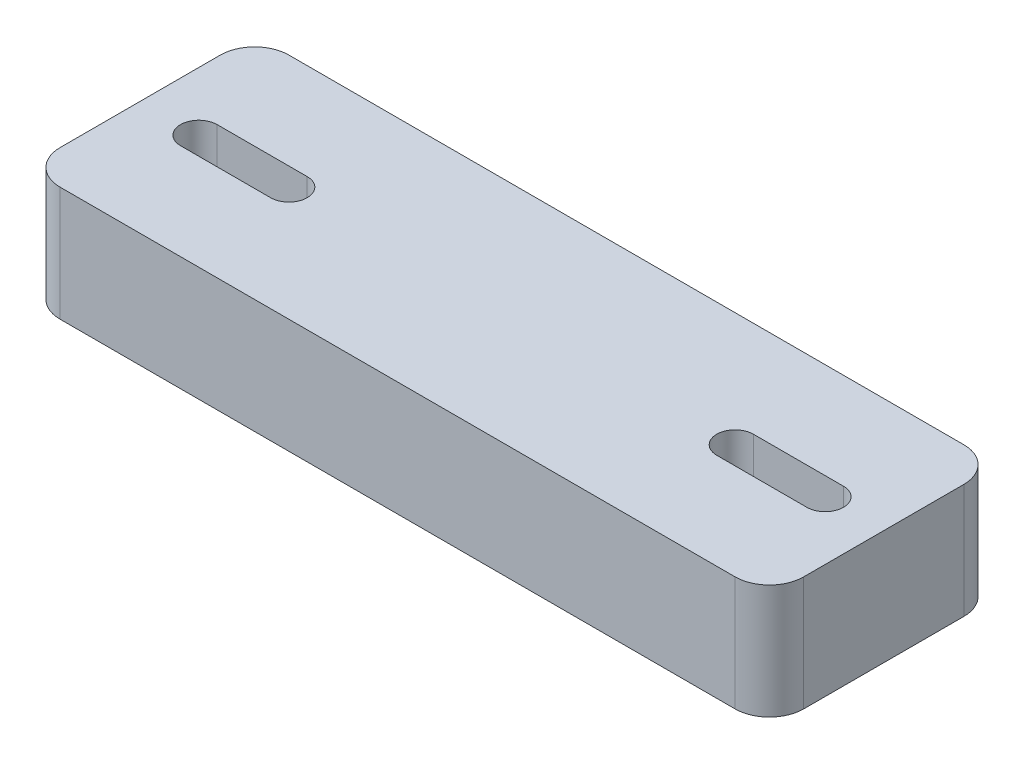
SolidWorks part; units mm, degrees
ref_plane "前视基准面" through (0, 0, 0) normal (0, 0, 1) x (1, 0, 0)
ref_plane "上视基准面" through (0, 0, 0) normal (0, 1, 0) x (1, 0, 0)
ref_plane "右视基准面" through (0, 0, 0) normal (1, 0, 0) x (0, 0, -1)
sketch "草图1" plane through (0, 0, 0) normal (0, 1, 0) x (1, 0, 0)
  line L1 (-32.5, 10) -> (32.5, 10)
  line L2 (-32.5, 10) -> (-32.5, -10)
  line L3 (-32.5, -10) -> (32.5, -10)
  line L4 (32.5, 10) -> (32.5, -10)
  line L5 (-32.5, 10) -> (32.5, -10) construction
  line L6 (-32.5, -10) -> (32.5, 10) construction
  point P0 (0, 0)
  dimension "D1" = 65
  dimension "D2" = 20
extrude "凸台-拉伸1" add sketch "草图1" along normal blind 10
sketch "草图2" plane through (0, 10, 0) normal (0, 1, 0) x (1, 0, 0)
  line L0 (0, 0) -> (0, -10) construction
  line L1 (-32.5, -10) -> (32.5, -10) construction
  line L2 (0, 0) -> (-32.5, 0) construction
  line L3 (-32.5, 10) -> (-32.5, -10) construction
  line L4 (-27.375, 0) -> (-19.5, 0) construction
  line L5 (-27.375, 1.6) -> (-19.5, 1.6)
  line L6 (-27.375, -1.6) -> (-19.5, -1.6)
  line L7 (27.375, 0) -> (19.5, 0) construction
  line L8 (27.375, 1.6) -> (19.5, 1.6)
  line L9 (27.375, -1.6) -> (19.5, -1.6)
  arc A0 (-27.375, 1.6) -> (-27.375, -1.6) centre (-27.375, 0) ccw
  arc A1 (-19.5, -1.6) -> (-19.5, 1.6) centre (-19.5, 0) ccw
  arc A2 (27.375, 1.6) -> (27.375, -1.6) centre (27.375, 0) cw
  arc A3 (19.5, -1.6) -> (19.5, 1.6) centre (19.5, 0) cw
  point P10 (-23.4375, 0)
  point P17 (23.4375, 0)
  dimension "D1" = 54.75
  dimension "D2" = 3.2
  dimension "D3" = 39
extrude "切除-拉伸1" cut sketch "草图2" against normal blind 10
fillet "圆角1" radius 3 4 edges at (-32.5, 5, -10) (-32.5, 5, 10) (32.5, 5, -10) (32.5, 5, 10)
